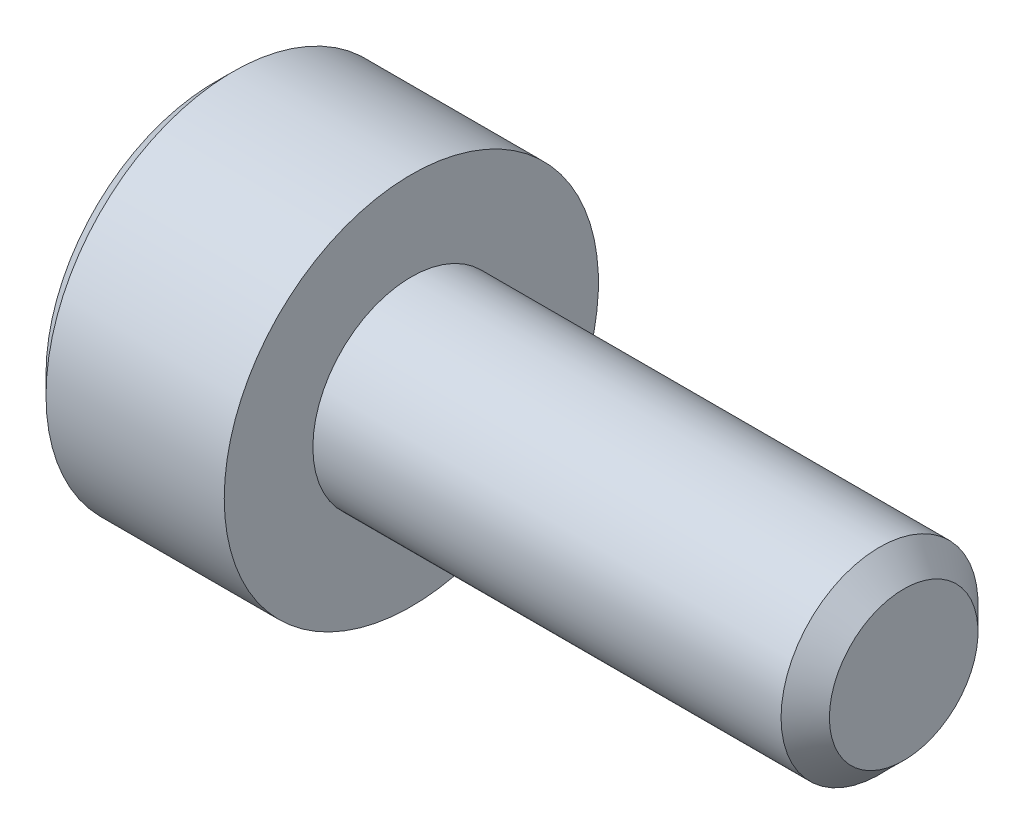
SolidWorks part; units mm, degrees
material "AISI 304"
ref_plane "正面" through (0, 0, 0) normal (0, 0, 1) x (1, 0, 0)
ref_plane "平面" through (0, 0, 0) normal (0, 1, 0) x (1, 0, 0)
ref_plane "右側面" through (0, 0, 0) normal (1, 0, 0) x (0, 0, -1)
ref_plane "Plane1" through (0, 0, 0) normal (0, 0, 1) x (1, 0, 0)
sketch "Sketch1" plane through (0, 0, 0) normal (0, 0, 1) x (1, 0, 0)
  line L0 (-2, 0) -> (-2, 1.71)
  line L1 (-2, 1.71) -> (-1.81, 1.9)
  line L2 (-1.81, 1.9) -> (0, 1.9)
  line L3 (0, 1.9) -> (0, 1)
  line L4 (0, 1) -> (4.7545, 1)
  line L5 (4.7545, 1) -> (5, 0.7545)
  line L6 (5, 0.7545) -> (5, 0)
  line L7 (5, 0) -> (-2, 0)
  line L8 (5, 0) -> (-2, 0) construction
revolve "Revolve1" add sketch "Sketch1" angle 360 about L8
cosmetic thread "Cosmetic Thread1" parameters "D1"=4.5748, "D2"=1.509
ref_plane "Plane2" through (-2, 0, 0) normal (1, 0, 0) x (0, 0, -1)
sketch "Sketch2" plane through (-2, 0, 0) normal (1, 0, 0) x (0, 0, -1)
  line L0 (-0.75, -0.433) -> (0, -0.866)
  line L1 (0, -0.866) -> (0.75, -0.433)
  line L2 (0.75, -0.433) -> (0.75, 0.433)
  line L3 (0.75, 0.433) -> (0, 0.866)
  line L4 (0, 0.866) -> (-0.75, 0.433)
  line L5 (-0.75, 0.433) -> (-0.75, -0.433)
extrude "Cut-Extrude1" cut sketch "Sketch2" along normal blind 0.8
